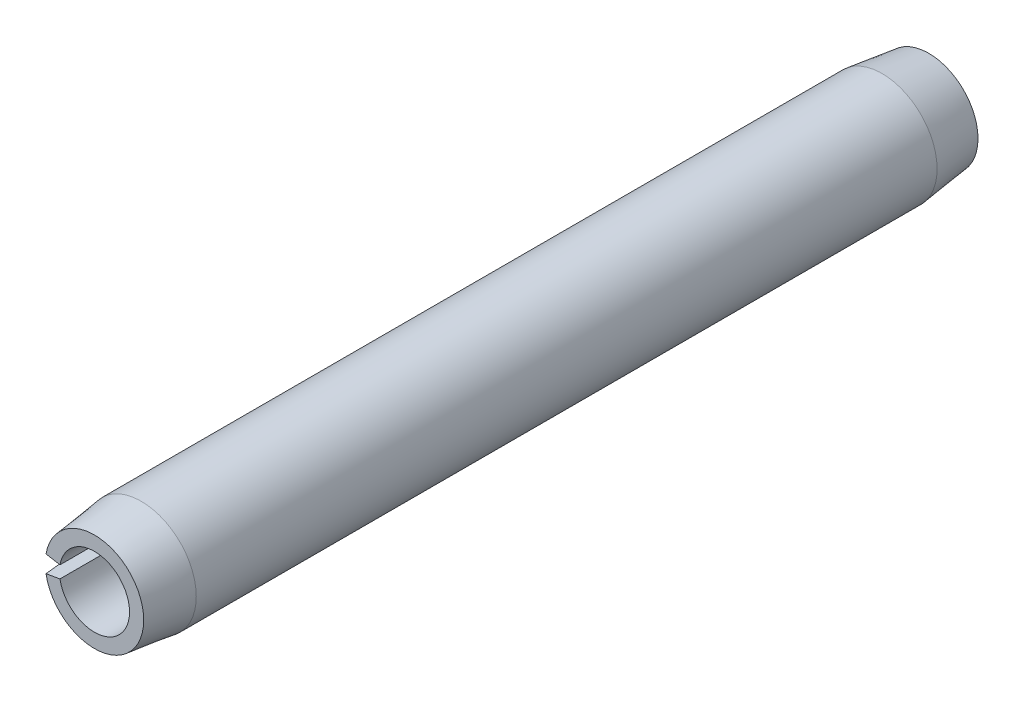
SolidWorks part; units mm, degrees
ref_plane "Front Plane" through (0, 0, 0) normal (0, 0, 1) x (1, 0, 0)
ref_plane "Top Plane" through (0, 0, 0) normal (0, 1, 0) x (1, 0, 0)
ref_plane "Right Plane" through (0, 0, 0) normal (1, 0, 0) x (0, 0, -1)
sketch "Sketch1" plane through (0, 0, 0) normal (0, 0, 1) x (1, 0, 0)
  line L0 (0.5334, 0) -> (0.8382, 0) construction
  line L1 (-0.8255, 0.1456) -> (-0.5253, 0.0926)
  line L2 (-0.5253, -0.0926) -> (-0.8255, -0.1456)
  arc A0 (-0.8255, -0.1456) -> (-0.8255, 0.1456) centre (0, 0) ccw
  arc A1 (-0.5253, -0.0926) -> (-0.5253, 0.0926) centre (0, 0) ccw
  dimension "OD" = 1.6764
  dimension "Wall thickness" = 0.3048
  dimension "D3" = 20
extrude "Extrude1" add sketch "Sketch1" along normal mid plane 12.7
sketch "Sketch2" plane through (0, 0, 0) normal (1, 0, 0) x (0, 0, -1)
  line L0 (0, -0.8382) -> (0, 0.8382) construction
  line L1 (6.35, 0) -> (-6.35, 0) construction
  line L2 (6.35, -0.5334) -> (6.35, 0.5334) construction
  line L3 (6.35, 0.8382) -> (-6.35, 0.8382) construction
  line L4 (6.35, 0.8382) -> (6.35, 0.7493)
  line L5 (6.35, 0.7493) -> (5.6388, 0.8382)
  line L6 (5.6388, 0.8382) -> (6.35, 0.8382)
  line L7 (6.35, -0.8382) -> (6.35, 0.8382) construction
  line L8 (-5.6388, 0.8382) -> (-6.35, 0.8382)
  line L9 (-6.35, 0.7493) -> (-5.6388, 0.8382)
  line L10 (-6.35, 0.8382) -> (-6.35, 0.7493)
  line L11 (5.6388, -0.8382) -> (6.35, -0.8382) construction
  line L12 (6.35, -0.7493) -> (5.6388, -0.8382) construction
  line L13 (6.35, -0.8382) -> (6.35, -0.7493) construction
  dimension "B" = 1.4986
  dimension "Chamfer max" = 0.7112
revolve "Cut-Revolve1" cut sketch "Sketch2" angle 360 about L1
sketch "Sketch3" plane through (0, 0, 0) normal (0, 0, 1) x (1, 0, 0)
  line L0 (0.5334, 0) -> (0.8382, 0) construction
  line L1 (0.5334, 0) -> (0.8382, 0)
  circle A0 centre (0, 0) radius 0.8382
  circle A1 centre (0, 0) radius 0.5334
  arc A2 (-0.8255, -0.1456) -> (-0.8255, 0.1456) centre (0, 0) ccw construction
  arc A3 (-0.5253, -0.0926) -> (-0.5253, 0.0926) centre (0, 0) ccw construction
